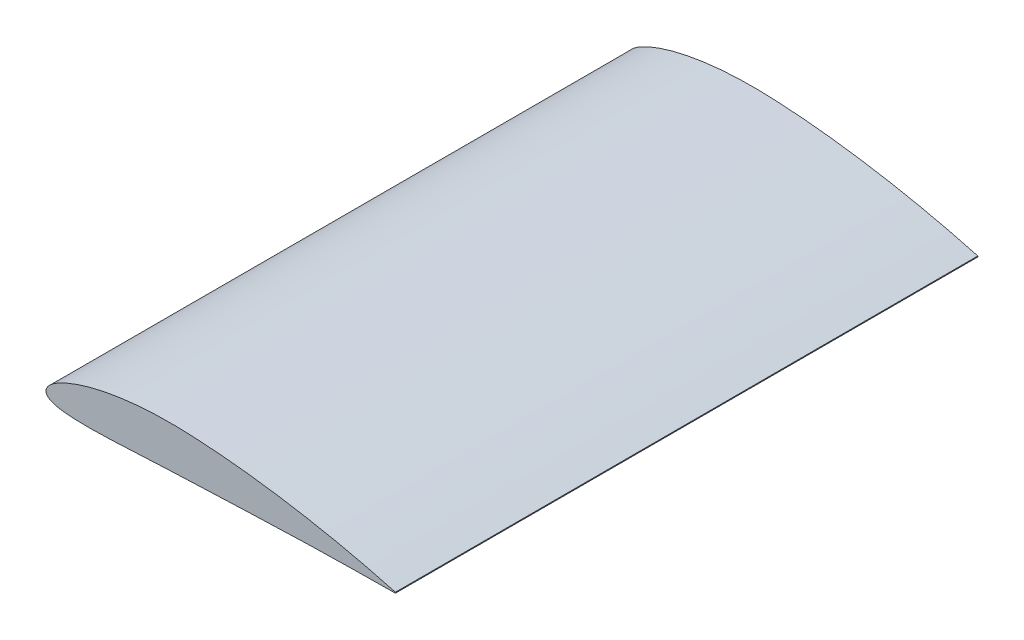
SolidWorks part; units mm, degrees
material "XPS"
ref_plane "Front Plane" through (0, 0, 0) normal (0, 0, 1) x (1, 0, 0)
ref_plane "Top Plane" through (0, 0, 0) normal (0, 1, 0) x (1, 0, 0)
ref_plane "Right Plane" through (0, 0, 0) normal (1, 0, 0) x (0, 0, -1)
curve "Кривая1"
  spline degree 3 poles (0.0025, -0.1472, 0) (0.0289, -0.4455, 0) (0.0833, -1.0612, 0) (0.4227, -1.9666, 0) (0.9763, -2.8381, 0) (1.7565, -3.6471, 0) (2.7491, -4.3932, 0) (3.9671, -5.0829, 0) (5.4423, -5.7284, 0) (7.2357, -6.3386, 0) (9.4428, -6.9184, 0) (12.2026, -7.4661, 0) (15.6905, -7.9675, 0) (20.0737, -8.3915, 0) (25.4279, -8.6968, 0) (31.68, -8.852, 0) (38.6369, -8.8515, 0) (46.0774, -8.7137, 0) (53.8291, -8.468, 0) (61.7839, -8.1437, 0) (69.8772, -7.7668, 0) (78.0625, -7.3594, 0) (86.2929, -6.9408, 0) (94.5257, -6.5276, 0) (102.7326, -6.1331, 0) (110.9185, -5.7659, 0) (119.106, -5.4384, 0) (127.3169, -5.1339, 0) (135.5631, -4.8037, 0) (143.8373, -4.4678, 0) (152.1286, -4.1281, 0) (160.4179, -3.7904, 0) (168.6982, -3.4589, 0) (176.9664, -3.1367, 0) (185.2231, -2.8268, 0) (193.4701, -2.5312, 0) (201.709, -2.252, 0) (209.9419, -1.9904, 0) (218.1703, -1.7477, 0) (226.3959, -1.5245, 0) (234.62, -1.3213, 0) (242.8434, -1.1383, 0) (251.0655, -0.9754, 0) (259.2802, -0.8323, 0) (267.4637, -0.7084, 0) (275.5412, -0.6035, 0) (283.3048, -0.5178, 0) (290.3769, -0.4518, 0) (295.8708, -0.4074, 0) (298.9446, -0.3855, 0) (300, -0.378, 0) knots 0 0 0 0 0.002952 0.006093 0.009451 0.013105 0.017146 0.021696 0.026922 0.033053 0.040418 0.04948 0.060872 0.075263 0.09303 0.113914 0.137123 0.161847 0.187529 0.213845 0.240604 0.26768 0.294919 0.322129 0.349225 0.376201 0.403191 0.430285 0.457483 0.484832 0.512206 0.539574 0.566902 0.594186 0.62143 0.64864 0.675822 0.702982 0.730125 0.757257 0.784384 0.811507 0.838629 0.865737 0.892784 0.919595 0.94565 0.969591 0.989559 1 1 1 1
curve "Кривая2"
  spline degree 3 poles (300, 0.378, 0) (298.9868, 0.654, 0) (296.0642, 1.4502, 0) (290.8696, 2.83, 0) (284.2197, 4.5452, 0) (276.9359, 6.3576, 0) (269.3471, 8.1754, 0) (261.6367, 9.9499, 0) (253.8749, 11.6637, 0) (246.0869, 13.3108, 0) (238.2816, 14.8894, 0) (230.4628, 16.3984, 0) (222.6331, 17.8369, 0) (214.7944, 19.2041, 0) (206.9485, 20.4989, 0) (199.0972, 21.7198, 0) (191.2424, 22.8654, 0) (183.3862, 23.9339, 0) (175.5305, 24.9231, 0) (167.6776, 25.8308, 0) (159.8302, 26.6544, 0) (151.9904, 27.3909, 0) (144.1641, 28.0368, 0) (136.3543, 28.5896, 0) (128.5833, 29.0403, 0) (120.8893, 29.3981, 0) (113.2941, 29.624, 0) (105.7871, 29.6881, 0) (98.3389, 29.5906, 0) (90.9366, 29.3292, 0) (83.5844, 28.8983, 0) (76.2905, 28.2936, 0) (69.0662, 27.5099, 0) (61.9269, 26.5429, 0) (54.8933, 25.3879, 0) (47.995, 24.0424, 0) (41.2775, 22.5076, 0) (34.8125, 20.7931, 0) (28.711, 18.9262, 0) (23.1248, 16.9611, 0) (18.2149, 14.98, 0) (14.0886, 13.0747, 0) (10.7512, 11.3155, 0) (8.1131, 9.7303, 0) (6.0405, 8.3096, 0) (4.406, 7.0251, 0) (3.1105, 5.8456, 0) (2.0858, 4.7431, 0) (1.2838, 3.6971, 0) (0.686, 2.6899, 0) (0.2589, 1.7169, 0) (0.1227, 1.0599, 0) (0.0576, 0.7457, 0) knots 0 0 0 0 0.010162 0.029313 0.052012 0.076619 0.101948 0.127526 0.153184 0.178868 0.204558 0.230246 0.255926 0.281594 0.307246 0.332878 0.358485 0.384061 0.409603 0.435104 0.460559 0.485959 0.511303 0.536552 0.561723 0.586629 0.611085 0.635251 0.659272 0.683164 0.706922 0.730536 0.753983 0.777235 0.800246 0.822951 0.845237 0.866916 0.887662 0.906968 0.924203 0.938879 0.950932 0.960693 0.968647 0.975233 0.980795 0.985584 0.989782 0.993521 0.996902 1 1 1 1
sketch "Эскиз1" plane through (0, 0, 0) normal (0, 0, 1) x (1, 0, 0)
  line L0 (0.0576, 0.7457) -> (0, 0)
  line L1 (0, 0) -> (0.0025, -0.1472)
  line L2 (300.1566, 0) -> (300.1566, 104.3192) construction
  line L3 (0, 0) -> (0, 190.298) construction
  line L4 (0, 0) -> (327.4735, 0) construction
  arc A0 (300, 0.378) -> (300, -0.378) centre (299.622, 0) cw
  spline S0 degree 3 poles (-1968.1899, -349.7333) (51.0828, 31.995) (-3.846, 9.4221) (0.4227, -1.9666) (0.9763, -2.8381) (1.7565, -3.6471) (2.7491, -4.3932) (3.9671, -5.0829) (5.4423, -5.7284) (7.2357, -6.3386) (9.4428, -6.9184) (12.2026, -7.4661) (15.6905, -7.9675) (20.0737, -8.3915) (25.4279, -8.6968) (31.68, -8.852) (38.6369, -8.8515) (46.0774, -8.7137) (53.8291, -8.468) (61.7839, -8.1437) (69.8772, -7.7668) (78.0625, -7.3594) (86.2929, -6.9408) (94.5257, -6.5276) (102.7326, -6.1331) (110.9185, -5.7659) (119.106, -5.4384) (127.3169, -5.1339) (135.5631, -4.8037) (143.8373, -4.4678) (152.1286, -4.1281) (160.4179, -3.7904) (168.6982, -3.4589) (176.9664, -3.1367) (185.2231, -2.8268) (193.4701, -2.5312) (201.709, -2.252) (209.9419, -1.9904) (218.1703, -1.7477) (226.3959, -1.5245) (234.62, -1.3213) (242.8434, -1.1383) (253.799, -0.9213) (264.7237, -0.7439) (275.5412, -0.6035) (283.3048, -0.5178) (290.3769, -0.4518) (482.2598, 1.0983) (671.8041, -8.4418) (845.2481, 1895.8073) knots -0.109425 -0.109425 -0.109425 -0.109425 0.002952 0.006093 0.009451 0.013105 0.017146 0.021696 0.026922 0.033053 0.040418 0.04948 0.060872 0.075263 0.09303 0.113914 0.137123 0.161847 0.187529 0.213845 0.240604 0.26768 0.294919 0.322129 0.349225 0.376201 0.403191 0.430285 0.457483 0.484832 0.512206 0.539574 0.566902 0.594186 0.62143 0.64864 0.675822 0.702982 0.730125 0.757257 0.784384 0.811507 0.838629 0.892784 0.919595 0.94565 0.969591 0.989559 2.843929 2.843929 2.843929 2.843929 only from (0.0025, -0.1472) to (300, -0.378) construction
  spline S1 degree 3 poles (1102.8776, 1823.6849) (485.687, -71.7459) (392.2937, -24.1102) (290.8696, 2.83) (284.2197, 4.5452) (276.9359, 6.3576) (269.3471, 8.1754) (261.6367, 9.9499) (253.8749, 11.6637) (246.0869, 13.3108) (238.2816, 14.8894) (230.4628, 16.3984) (222.6331, 17.8369) (214.7944, 19.2041) (206.9485, 20.4989) (199.0972, 21.7198) (191.2424, 22.8654) (183.3862, 23.9339) (175.5305, 24.9231) (167.6776, 25.8308) (159.8302, 26.6544) (151.9904, 27.3909) (144.1641, 28.0368) (136.3543, 28.5896) (128.5833, 29.0403) (120.8893, 29.3981) (113.2941, 29.624) (105.7871, 29.6881) (98.3389, 29.5906) (90.9366, 29.3292) (83.5844, 28.8983) (76.2905, 28.2936) (69.0662, 27.5099) (61.9269, 26.5429) (54.8933, 25.3879) (47.995, 24.0424) (41.2775, 22.5076) (34.8125, 20.7931) (28.711, 18.9262) (23.1248, 16.9611) (18.2149, 14.98) (14.0886, 13.0747) (10.7512, 11.3155) (8.1131, 9.7303) (6.0405, 8.3096) (4.406, 7.0251) (3.1105, 5.8456) (2.0858, 4.7431) (1.2838, 3.6971) (0.686, 2.6899) (-4.8757, -9.982) (43.3386, -38.3003) (-1926.5399, 536.0326) knots -0.963508 -0.963508 -0.963508 -0.963508 0.010162 0.029313 0.052012 0.076619 0.101948 0.127526 0.153184 0.178868 0.204558 0.230246 0.255926 0.281594 0.307246 0.332878 0.358485 0.384061 0.409603 0.435104 0.460559 0.485959 0.511303 0.536552 0.561723 0.586629 0.611085 0.635251 0.659272 0.683164 0.706922 0.730536 0.753983 0.777235 0.800246 0.822951 0.845237 0.866916 0.887662 0.906968 0.924203 0.938879 0.950932 0.960693 0.968647 0.975233 0.980795 0.985584 0.989782 0.993521 0.996902 1.122862 1.122862 1.122862 1.122862 only from (300, 0.378) to (0.0576, 0.7457) construction
  spline S2 degree 3 poles (0.0025, -0.1472) (0.0289, -0.4455) (0.0833, -1.0612) (0.4227, -1.9666) (0.9763, -2.8381) (1.7565, -3.6471) (2.7491, -4.3932) (3.9671, -5.0829) (5.4423, -5.7284) (7.2357, -6.3386) (9.4428, -6.9184) (12.2026, -7.4661) (15.6905, -7.9675) (20.0737, -8.3915) (25.4279, -8.6968) (31.68, -8.852) (38.6369, -8.8515) (46.0774, -8.7137) (53.8291, -8.468) (61.7839, -8.1437) (69.8772, -7.7668) (78.0625, -7.3594) (86.2929, -6.9408) (94.5257, -6.5276) (102.7326, -6.1331) (110.9185, -5.7659) (119.106, -5.4384) (127.3169, -5.1339) (135.5631, -4.8037) (143.8373, -4.4678) (152.1286, -4.1281) (160.4179, -3.7904) (168.6982, -3.4589) (176.9664, -3.1367) (185.2231, -2.8268) (193.4701, -2.5312) (201.709, -2.252) (209.9419, -1.9904) (218.1703, -1.7477) (226.3959, -1.5245) (234.62, -1.3213) (242.8434, -1.1383) (253.799, -0.9213) (264.7237, -0.7439) (275.5412, -0.6035) (283.3048, -0.5178) (290.3769, -0.4518) (295.8708, -0.4074) (298.9446, -0.3855) (300, -0.378) knots 0 0 0 0 0.002952 0.006093 0.009451 0.013105 0.017146 0.021696 0.026922 0.033053 0.040418 0.04948 0.060872 0.075263 0.09303 0.113914 0.137123 0.161847 0.187529 0.213845 0.240604 0.26768 0.294919 0.322129 0.349225 0.376201 0.403191 0.430285 0.457483 0.484832 0.512206 0.539574 0.566902 0.594186 0.62143 0.64864 0.675822 0.702982 0.730125 0.757257 0.784384 0.811507 0.838629 0.892784 0.919595 0.94565 0.969591 0.989559 1 1 1 1
  spline S3 degree 3 poles (300, 0.378) (298.9868, 0.654) (296.0642, 1.4502) (290.8696, 2.83) (284.2197, 4.5452) (276.9359, 6.3576) (269.3471, 8.1754) (261.6367, 9.9499) (253.8749, 11.6637) (246.0869, 13.3108) (238.2816, 14.8894) (230.4628, 16.3984) (222.6331, 17.8369) (214.7944, 19.2041) (206.9485, 20.4989) (199.0972, 21.7198) (191.2424, 22.8654) (183.3862, 23.9339) (175.5305, 24.9231) (167.6776, 25.8308) (159.8302, 26.6544) (151.9904, 27.3909) (144.1641, 28.0368) (136.3543, 28.5896) (128.5833, 29.0403) (120.8893, 29.3981) (113.2941, 29.624) (105.7871, 29.6881) (98.3389, 29.5906) (90.9366, 29.3292) (83.5844, 28.8983) (76.2905, 28.2936) (69.0662, 27.5099) (61.9269, 26.5429) (54.8933, 25.3879) (47.995, 24.0424) (41.2775, 22.5076) (34.8125, 20.7931) (28.711, 18.9262) (23.1248, 16.9611) (18.2149, 14.98) (14.0886, 13.0747) (10.7512, 11.3155) (8.1131, 9.7303) (6.0405, 8.3096) (4.406, 7.0251) (3.1105, 5.8456) (2.0858, 4.7431) (1.2838, 3.6971) (0.686, 2.6899) (0.2589, 1.7169) (0.1227, 1.0599) (0.0576, 0.7457) knots 0 0 0 0 0.010162 0.029313 0.052012 0.076619 0.101948 0.127526 0.153184 0.178868 0.204558 0.230246 0.255926 0.281594 0.307246 0.332878 0.358485 0.384061 0.409603 0.435104 0.460559 0.485959 0.511303 0.536552 0.561723 0.586629 0.611085 0.635251 0.659272 0.683164 0.706922 0.730536 0.753983 0.777235 0.800246 0.822951 0.845237 0.866916 0.887662 0.906968 0.924203 0.938879 0.950932 0.960693 0.968647 0.975233 0.980795 0.985584 0.989782 0.993521 0.996902 1 1 1 1
  dimension "D1" = 0.5346
  dimension "D2" = 300.1566
extrude "Бобышка-Вытянуть1" add sketch "Эскиз1" along normal mid plane 500
